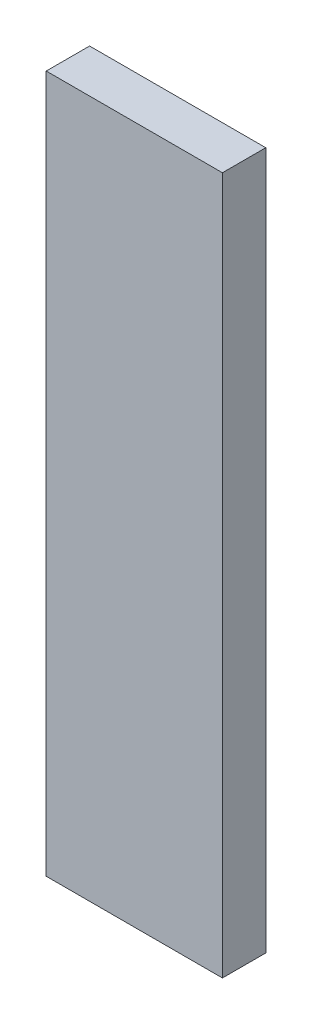
SolidWorks part; units mm, degrees
ref_plane "Front Plane" through (0, 0, 0) normal (0, 0, 1) x (1, 0, 0)
ref_plane "Top Plane" through (0, 0, 0) normal (0, 1, 0) x (1, 0, 0)
ref_plane "Right Plane" through (0, 0, 0) normal (1, 0, 0) x (0, 0, -1)
sketch "Sketch1" plane through (0, 0, 0) normal (0, 0, 1) x (1, 0, 0)
  line L0 (-37.5648, 18.053) -> (-32.4024, 18.053)
  line L3 (-37.5648, -2.382) -> (-37.5648, 18.053)
  line L6 (-37.5648, 18.053) -> (-32.4024, 18.053)
  line L7 (-37.5648, 18.053) -> (-37.5648, -2.382)
  line L8 (-37.5648, -2.382) -> (-32.4024, -2.382)
  line L9 (-32.4024, 18.053) -> (-32.4024, -2.382)
  line L12 (-32.4024, 16.6244) -> (-32.4024, -2.382)
  line L15 (-32.4024, -2.382) -> (-37.5648, -2.382)
extrude "Boss-Extrude1" add sketch "Sketch1" along normal blind 1.27 contours L7 L6 L9 L8
sketch "Sketch2" plane through (-37.5648, 0, 0) normal (-1, 0, 0) x (0, 0, 1)
  line L10 (0.1917, 16.874) -> (1.0307, 16.874)
  line L11 (0.1917, 16.874) -> (0.1917, 12.9918)
  line L12 (0.1917, 12.9918) -> (1.0307, 12.9918)
  line L13 (1.0307, 16.874) -> (1.0307, 12.9918)
extrude "Cut-Extrude1" cut sketch "Sketch2" against normal blind 3.81
